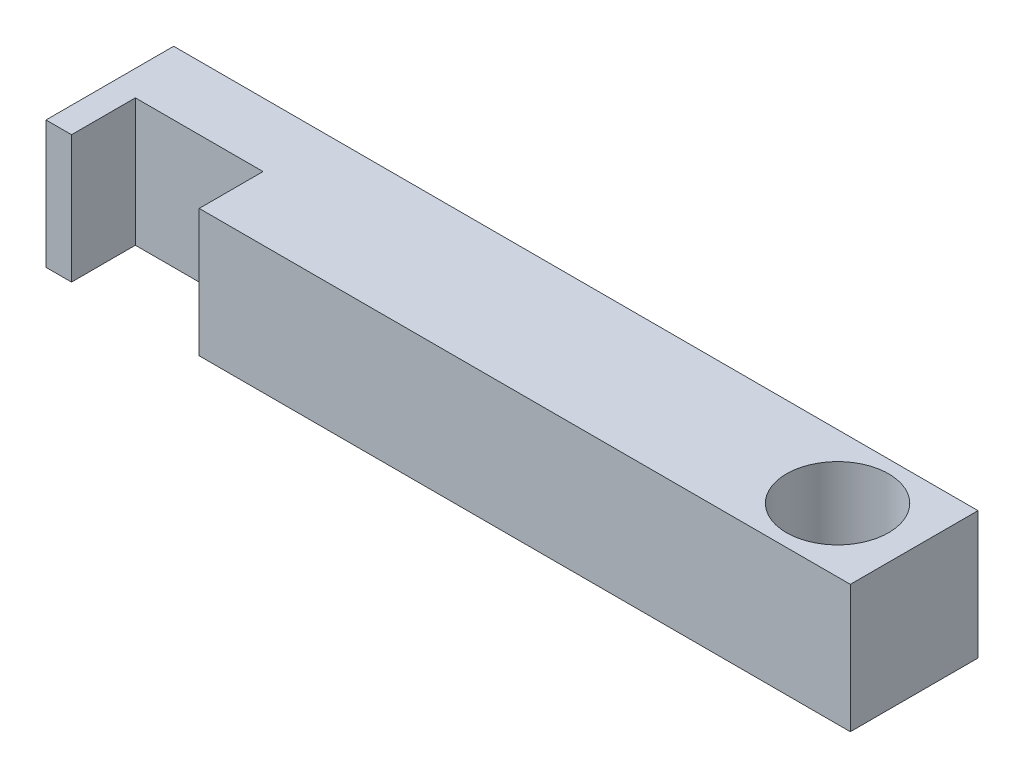
SolidWorks part; units mm, degrees
ref_plane "前基準面" through (0, 0, 0) normal (0, 0, 1) x (1, 0, 0)
ref_plane "上基準面" through (0, 0, 0) normal (0, 1, 0) x (1, 0, 0)
ref_plane "右基準面" through (0, 0, 0) normal (1, 0, 0) x (0, 0, -1)
sketch "草圖1" plane through (0, 0, 0) normal (0, 1, 0) x (1, 0, 0)
  line L0 (-55, -5) -> (-55, 0)
  line L1 (-57, 5) -> (6, 5)
  line L2 (-57, 5) -> (-57, -5)
  line L3 (-57, -5) -> (-55, -5)
  line L4 (6, 5) -> (6, -5)
  line L5 (-55, 0) -> (-45, 0)
  line L6 (-45, 0) -> (-45, -5)
  line L7 (-45, -5) -> (6, -5)
  circle A0 centre (0, 0) radius 4
  point P8 (6, 0)
  dimension "D1" = 6
  dimension "hole" = 8
  dimension "D2" = 10
  dimension "length" = 63
  dimension "D4" = 5
  dimension "D5" = 10
  dimension "D6" = 2
extrude "填料-伸長1" add sketch "草圖1" along normal mid plane 10
